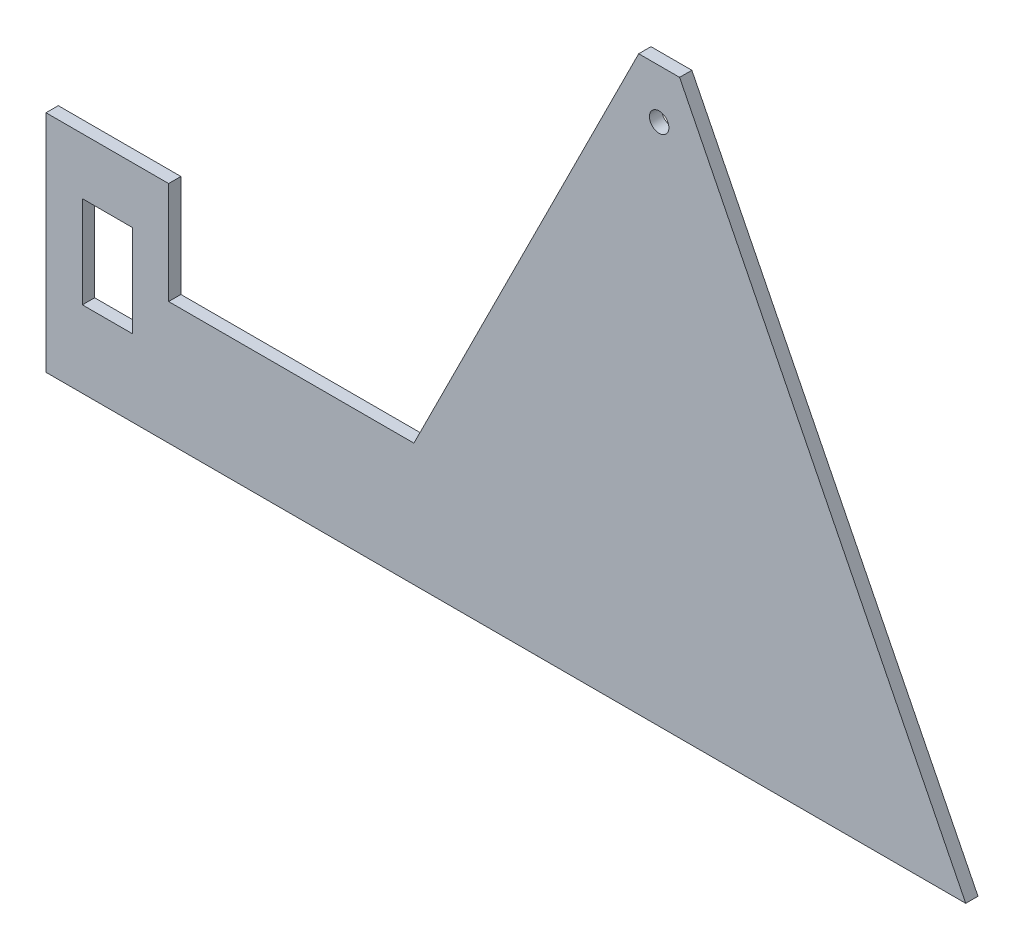
SolidWorks part; units mm, degrees
material "Balsa"
ref_plane "Alzado" through (0, 0, 0) normal (0, 0, 1) x (1, 0, 0)
ref_plane "Planta" through (0, 0, 0) normal (0, 1, 0) x (1, 0, 0)
ref_plane "Vista lateral" through (0, 0, 0) normal (1, 0, 0) x (0, 0, -1)
sketch "Croquis1" plane through (0, 0, 0) normal (0, 0, 1) x (1, 0, 0)
  line L0 (0, 150) -> (0, -176.1405) construction
  line L1 (-146.095, 0) -> (168.9269, 0) construction
  line L2 (75, 0) -> (-75, 0)
  line L3 (-60, 30) -> (0, 150)
  line L4 (75, 0) -> (0, 150)
  line L5 (-75, 0) -> (-150, 0)
  line L6 (-150, 0) -> (-150, 30)
  line L7 (-120, 30) -> (-60, 30)
  line L8 (-150, 30) -> (-150, 55)
  line L9 (-150, 55) -> (-120, 55)
  line L10 (-120, 55) -> (-120, 30)
  line L11 (-135, 55) -> (-135, -15.9615) construction
  line L12 (-75, 0) -> (0, 150) construction
  line L13 (-60, 30) -> (-188.778, 30) construction
  line L14 (-141.1, 41.25) -> (-128.9, 41.25)
  line L15 (-141.1, 41.25) -> (-141.1, 18.75)
  line L16 (-141.1, 18.75) -> (-128.9, 18.75)
  line L17 (-128.9, 41.25) -> (-128.9, 18.75)
  line L18 (-141.1, 41.25) -> (-128.9, 18.75) construction
  line L19 (-141.1, 18.75) -> (-128.9, 41.25) construction
  point P6 (-120, 42.5)
  point P9 (0, 0)
  point P17 (-135, 30)
  dimension "D7" = 22.5
  dimension "D1" = 75
  dimension "D2" = 150
  dimension "D3" = 30
  dimension "D4" = 150
  dimension "D5" = 25
  dimension "D6" = 30
  dimension "D8" = 12.2
extrude "Saliente-Extruir1" add sketch "Croquis1" along normal blind 3
sketch "Croquis2" plane through (0, 0, 0) normal (0, 0, 1) x (1, 0, 0)
  line L0 (-34.6969, 128) -> (31.6762, 128) construction
  line L1 (0, -14.0881) -> (0, 160.498) construction
  line L2 (75, 0) -> (0, 150) construction
  line L3 (0, 150) -> (-60, 30) construction
  line L4 (5, 140) -> (0, 150)
  line L5 (0, 150) -> (-5, 140)
  line L6 (-5, 140) -> (5, 140)
  circle A0 centre (0, 128) radius 2.3812
  dimension "D3" = 4.7625
  dimension "D1" = 10
  dimension "D2" = 12
extrude "Cortar-Extruir1" cut sketch "Croquis2" along normal through all
